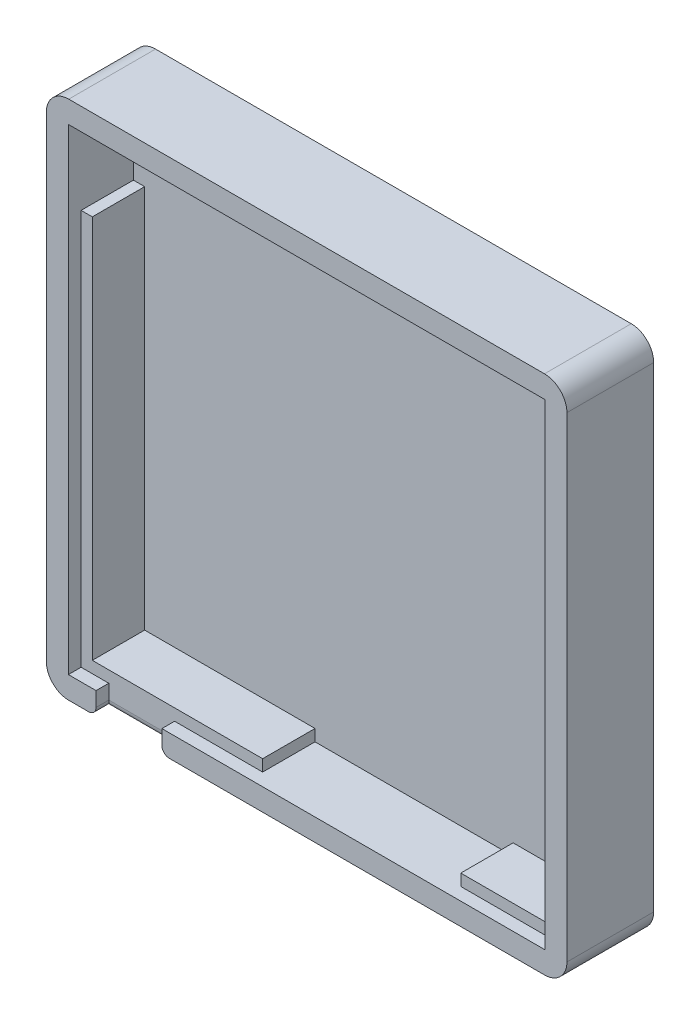
SolidWorks part; units mm, degrees
ref_plane "Front Plane" through (0, 0, 0) normal (0, 0, 1) x (1, 0, 0)
ref_plane "Top Plane" through (0, 0, 0) normal (0, 1, 0) x (1, 0, 0)
ref_plane "Right Plane" through (0, 0, 0) normal (1, 0, 0) x (0, 0, -1)
sketch "Sketch1" plane through (0, 0, 0) normal (0, 0, 1) x (1, 0, 0)
  line L1 (0, 0) -> (69.6, 0)
  line L2 (0, 0) -> (0, 69.6)
  line L3 (0, 69.6) -> (69.6, 69.6)
  line L4 (69.6, 0) -> (69.6, 69.6)
  dimension "D1" = 69.6
  dimension "D2" = 69.6
extrude "Boss-Extrude1" add sketch "Sketch1" along normal blind 11.6
sketch "Sketch2" plane through (0, 0, 11.6) normal (0, 0, 1) x (1, 0, 0)
  line L0 (4.45, 34.8) -> (0, 34.8) construction
  line L1 (4.45, 65.1) -> (65.15, 65.1)
  line L2 (4.45, 65.1) -> (4.45, 4.5)
  line L3 (4.45, 4.5) -> (65.15, 4.5)
  line L4 (65.15, 65.1) -> (65.15, 4.5)
  line L5 (0, 69.6) -> (0, 0) construction
  line L6 (65.15, 34.8) -> (69.6, 34.8) construction
  line L8 (69.6, 0) -> (69.6, 69.6) construction
  dimension "D1" = 60.7
  dimension "D2" = 60.6
extrude "Cut-Extrude3" cut sketch "Sketch2" against normal blind 8.7
sketch "Sketch4" plane through (0, 0, 11.6) normal (0, 0, 1) x (1, 0, 0)
  line L0 (66.65, 34.8) -> (69.6, 34.8) construction
  line L1 (66.65, 2.95) -> (2.95, 2.95)
  line L2 (66.65, 2.95) -> (66.65, 66.65)
  line L3 (66.65, 66.65) -> (2.95, 66.65)
  line L4 (2.95, 2.95) -> (2.95, 66.65)
  line L5 (69.6, 0) -> (69.6, 69.6) construction
  line L6 (2.95, 34.8) -> (0, 34.8) construction
  line L7 (0, 69.6) -> (0, 0) construction
  dimension "D1" = 63.7
extrude "Cut-Extrude4" cut sketch "Sketch4" against normal blind 1.7
sketch "Sketch5" plane through (0, 0, 11.6) normal (0, 0, 1) x (1, 0, 0)
  line L1 (15.45, 2.95) -> (6.65, 2.95)
  line L2 (15.45, 2.95) -> (15.45, 0)
  line L3 (15.45, 0) -> (6.65, 0)
  line L4 (6.65, 2.95) -> (6.65, 0)
  line L5 (0, 0) -> (69.6, 0) construction
  line L6 (2.95, 2.95) -> (66.65, 2.95) construction
  line L7 (2.95, 66.65) -> (2.95, 2.95) construction
  point P4 (15.45, 1.475)
  point P5 (6.65, 1.475)
  point P6 (9.7373, 5.204)
  dimension "D1" = 8.8
  dimension "D2" = 3.7
extrude "Cut-Extrude5" cut sketch "Sketch5" against normal blind 1.7
sketch "Sketch6" plane through (0, 0, 9.9) normal (0, 0, 1) x (1, 0, 0)
  line L0 (15.45, 2.95) -> (66.65, 2.95) construction
  line L5 (2.95, 66.65) -> (13.0401, 66.65)
  line L6 (2.95, 66.65) -> (2.95, 55.8475)
  line L7 (2.95, 55.8475) -> (13.0401, 55.8475)
  line L8 (13.0401, 66.65) -> (13.0401, 55.8475)
  line L9 (53.7103, 2.95) -> (27.2229, 2.95)
  line L10 (53.7103, 2.95) -> (53.7103, 6.564)
  line L11 (53.7103, 6.564) -> (27.2229, 6.564)
  line L12 (27.2229, 2.95) -> (27.2229, 6.564)
  line L14 (66.65, 66.65) -> (56.7541, 66.65)
  line L15 (66.65, 66.65) -> (66.65, 55.8475)
  line L16 (66.65, 55.8475) -> (56.7541, 55.8475)
  line L17 (56.7541, 66.65) -> (56.7541, 55.8475)
extrude "Cut-Extrude6" cut sketch "Sketch6" against normal blind 7
fillet "Fillet1" radius 3 4 edges at (69.6, 69.6, 5.8) (0, 69.6, 5.8) (0, 0, 5.8) (69.6, 0, 5.8)
fillet "Fillet2" radius 1 3 edges at (6.65, 0, 10.75) (11.05, 0, 9.9) (15.45, 0, 10.75)
